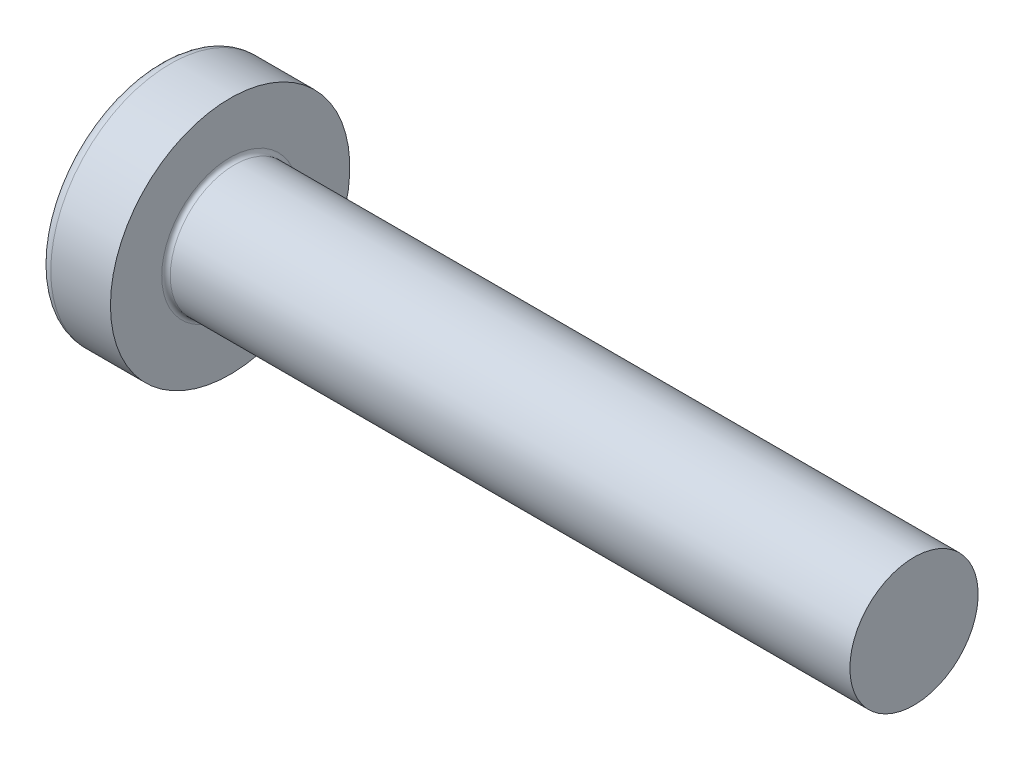
SolidWorks part; units mm, degrees
ref_plane "Plane1" through (0, 0, 0) normal (0, 0, 1) x (1, 0, 0)
ref_plane "Plane2" through (0, 0, 0) normal (0, 1, 0) x (1, 0, 0)
ref_plane "Plane3" through (0, 0, 0) normal (1, 0, 0) x (0, 0, -1)
sketch "BodySke" plane through (0, 0, 0) normal (0, 0, 1) x (1, 0, 0)
  line L0 (2.4, 1.5) -> (2.4, 2.8)
  line L1 (2.65, 6.35) -> (2.65, -3.175) construction
  line L2 (-25.4, 0) -> (127, 0) construction
  line L3 (18.4, 0) -> (0, 0)
  line L4 (2.4, 1.5) -> (18.4, 1.5)
  line L5 (18.4, 1.5) -> (18.4, 0)
  line L6 (1.0035, 2.8) -> (2.4, 2.8)
  line L8 (2.4, 6.35) -> (2.4, -3.175) construction
  arc A0 (0.7754, 2.6744) -> (0, 0) centre (5, 0) ccw
  arc A2 (0.7754, 2.6744) -> (1.0035, 2.8) centre (1.0035, 2.53) cw
  dimension "Head_crown_rad" = 5
  dimension "Head_fillet_rad" = 0.27
  dimension "Length" = 16
  dimension "Head_ht" = 2.4
  dimension "Head_dia" = 5.6
  dimension "Advance" = 0.5
  dimension "Thread_nom" = 16
  dimension "Diameter" = 3
revolve "Base-Revolve" add sketch "BodySke"
cosmetic thread "ThreadCosmetic" [suppressed]
fillet "Fillet1" radius 0.1 1 edges at (2.4, 0, 1.5)
sketch "Sketch3" plane through (0, 0, 0) normal (1, 0, 0) x (0, 0, -1)
  line L0 (0.37, -1.4) -> (-0.37, -1.4)
  line L1 (0.37, -1.4) -> (0.37, 1.4)
  line L2 (-0.37, 1.4) -> (0.37, 1.4)
  line L3 (-0.37, 1.4) -> (-0.37, -1.4)
  dimension "Cross_dia" = 2.8
  dimension "D1" = 1.4
  dimension "Cross_width" = 0.74
  dimension "D2" = 0.37
ref_plane "Plane4" through (1.75, 0, 0) normal (1, 0, 0) x (0, 0, -1)
sketch "Sketch4" plane through (1.75, 0, 0) normal (1, 0, 0) x (0, 0, -1)
  line L0 (0.37, -0.5275) -> (-0.37, -0.5275)
  line L1 (0.37, -0.5275) -> (0.37, 0.5275)
  line L2 (-0.37, 0.5275) -> (0.37, 0.5275)
  line L3 (-0.37, 0.5275) -> (-0.37, -0.5275)
  dimension "D1" = 0.74
  dimension "D2" = 1.055
  dimension "D3" = 0.37
  dimension "D4" = 0.5275
loft "Recess" cut profiles "Sketch3", "Sketch4"
pattern_circular "RecPat" count 2 every 90 about axis through (0, 0, 0) along (1, 0, 0) of "Recess"
sketch "RecCorSke" plane through (0, 0, 0) normal (0, 0, 1) x (1, 0, 0)
  line L0 (-3.175, 0) -> (15.875, 0) construction
  line L1 (-25.4, 0) -> (127, 0) construction
  line L2 (0, 0) -> (0, 0.6784)
  line L3 (0, 0.6784) -> (1.75, 0.556)
  line L4 (1.75, 0.556) -> (1.9307, 0)
  line L5 (1.9307, 0) -> (0, 0)
  dimension "Diameter" = 1.112
  dimension "Depth" = 1.75
  dimension "Draft_angle" = 4
  dimension "Bottom_angle" = 18
revolve "RecessCore" cut sketch "RecCorSke" angle 360 about L0
sketch "ThdSchSke" plane through (0, 0, 0) normal (0, 0, 1) x (1, 0, 0)
  line L0 (3.4, -1.2195) -> (3.2036, -1.5)
  line L1 (3.4, -1.2195) -> (3.5964, -1.5)
  line L2 (3.5964, -1.5) -> (3.5964, -1.875)
  line L3 (-3.175, 0) -> (5.1513, 0) construction
  line L5 (3.5964, -1.875) -> (3.2036, -1.875)
  line L6 (3.2036, -1.875) -> (3.2036, -1.5)
  dimension "Diameter" = 3
  dimension "SideAngle" = 55
  dimension "VeeAngle" = 70
  dimension "Thread_minor" = 2.439
  dimension "Overcut" = 3.75
  dimension "Start" = 3.4
revolve "ThreadSchematic" [suppressed] cut sketch "ThdSchSke" angle 360 about L3
pattern_linear "ThdSchPat" [suppressed]
equation "\"D1@Sketch3\" = \"Cross_dia@Sketch3\" / 2"
equation "\"D2@Sketch3\" = \"Cross_width@Sketch3\" / 2"
equation "\"Depth@RecCorSke\" = \"Cross_depth@Plane4\""
equation "\"D1@Sketch4\" = \"Cross_width@Sketch3\""
equation "\"D2@Sketch4\" = \"Cross_dia@Sketch3\" - 2.0 * \"Cross_depth@Plane4\" * tan(26.5  * 0.017453292)"
equation "\"D3@Sketch4\" = \"D1@Sketch4\" / 2"
equation "\"D4@Sketch4\" = \"D2@Sketch4\" / 2"
equation "\"Thread_length@ThreadCosmetic\" = ((sgn( (\"Length@BodySke\" - \"Advance@BodySke\" * 2.0 ) - \"Thread_nom@BodySke\" )-1)*( (\"Length@BodySke\" - \"Advance@BodySke\" * 2.0 ) - \"Thread_nom@BodySke\" ))/-2+ \"Thread_nom@BodySke\""
equation "\"Thread_minor@ThdSchSke\" = \"Thread_minor@ThreadCosmetic\""
equation "\"Diameter@ThdSchSke\" = \"Diameter@BodySke\""
equation "\"Overcut@ThdSchSke\" = \"Diameter@BodySke\" * 1.25"
equation "\"Start@ThdSchSke\" = \"Head_ht@BodySke\" + \"Length@BodySke\" - \"Thread_length@ThreadCosmetic\"  '---Non-countersunk---"
equation "\"Num_threads@ThdSchPat\" = int( \"Thread_length@ThreadCosmetic\" / \"Advance@BodySke\" + 0.999 )  + 1"
equation "\"Advance@ThdSchPat\" = \"Thread_length@ThreadCosmetic\" /  (\"Num_threads@ThdSchPat\" - 1) 'relax it"
